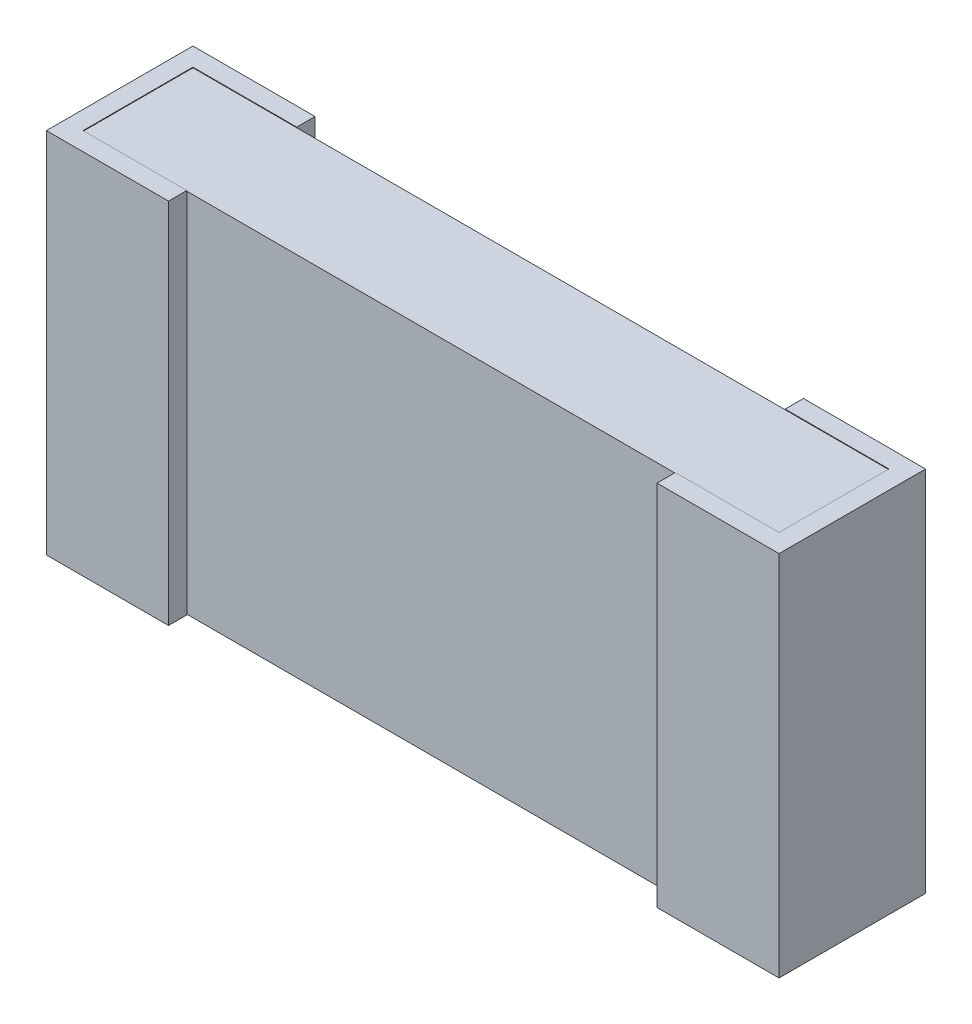
SolidWorks part; units mm, degrees
ref_plane "x/y" through (0, 0, 0) normal (0, 0, 1) x (1, 0, 0)
ref_plane "x/z" through (0, 0, 0) normal (0, 1, 0) x (1, 0, 0)
ref_plane "y/z" through (0, 0, 0) normal (1, 0, 0) x (0, 0, -1)
sketch "Sketch2" plane through (0, 0, 0) normal (0, 1, 0) x (1, 0, 0)
  line L0 (0.0762, -0.5334) -> (2.9718, -0.5334)
  line L1 (0.0762, -0.5334) -> (0.0762, -0.0762)
  line L2 (2.9718, -0.0762) -> (0.0762, -0.0762)
  line L3 (2.9718, -0.0762) -> (2.9718, -0.5334)
  dimension "D1" = 2.8956
  dimension "D2" = 0.4572
  dimension "D3" = 0.0762
extrude "Base-Extrude" add sketch "Sketch2" along normal mid plane 1.524
ref_plane "Plane4" through (0, 0.7645, 0) normal (0, 1, 0) x (-1, 0, 0)
sketch "Sketch3" plane through (0, 0.7645, 0) normal (0, 1, 0) x (-1, 0, 0)
  line L0 (-0.508, 0.6096) -> (-0.508, 0.5334)
  line L1 (-0.0762, 0.5334) -> (-2.9718, 0.5334) construction
  line L2 (-0.508, 0) -> (0, 0)
  line L3 (0, 0) -> (0, 0.6096)
  line L4 (0, 0.6096) -> (-0.508, 0.6096)
  line L5 (-0.508, 0.0762) -> (-0.508, 0)
  line L6 (-0.508, 0.0762) -> (-0.0762, 0.0762)
  line L7 (-0.0762, 0.0762) -> (-0.0762, 0.5334)
  line L8 (-0.0762, 0.5334) -> (-0.508, 0.5334)
  dimension "D1" = 0.508
  dimension "D2" = 0.508
extrude "Boss-Extrude8" add sketch "Sketch3" against normal blind 1.5291
ref_plane "Plane6" through (1.524, 0, 0) normal (1, 0, 0) x (0, 0, -1)
mirror "Mirror5" about plane through (1.524, 0, 0) normal (1, 0, 0)
